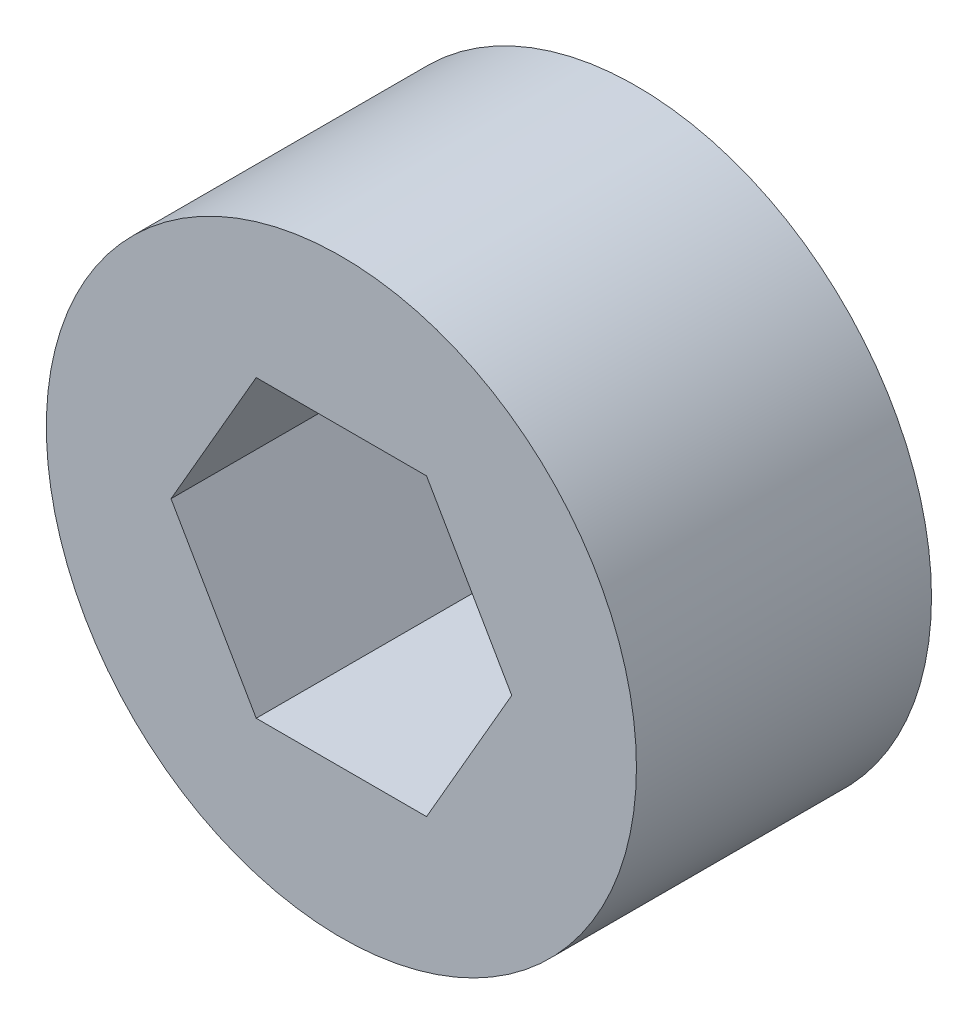
SolidWorks part; units mm, degrees
ref_plane "Front Plane" through (0, 0, 0) normal (0, 0, 1) x (1, 0, 0)
ref_plane "Top Plane" through (0, 0, 0) normal (0, 1, 0) x (1, 0, 0)
ref_plane "Right Plane" through (0, 0, 0) normal (1, 0, 0) x (0, 0, -1)
sketch "Sketch1" plane through (0, 0, 0) normal (0, 0, 1) x (1, 0, 0)
  line L1 (7.3323, 0) -> (3.6662, 6.35)
  line L2 (3.6662, 6.35) -> (-3.6662, 6.35)
  line L3 (-3.6662, 6.35) -> (-7.3323, 0)
  line L4 (-7.3323, 0) -> (-3.6662, -6.35)
  line L5 (-3.6662, -6.35) -> (3.6662, -6.35)
  line L6 (3.6662, -6.35) -> (7.3323, 0)
  circle A0 centre (0, 0) radius 6.35 construction
  circle A1 centre (0, 0) radius 12.7
  dimension "D2" = 25.4
  dimension "D1" = 12.7
extrude "Boss-Extrude1" add sketch "Sketch1" along normal blind 12.7
